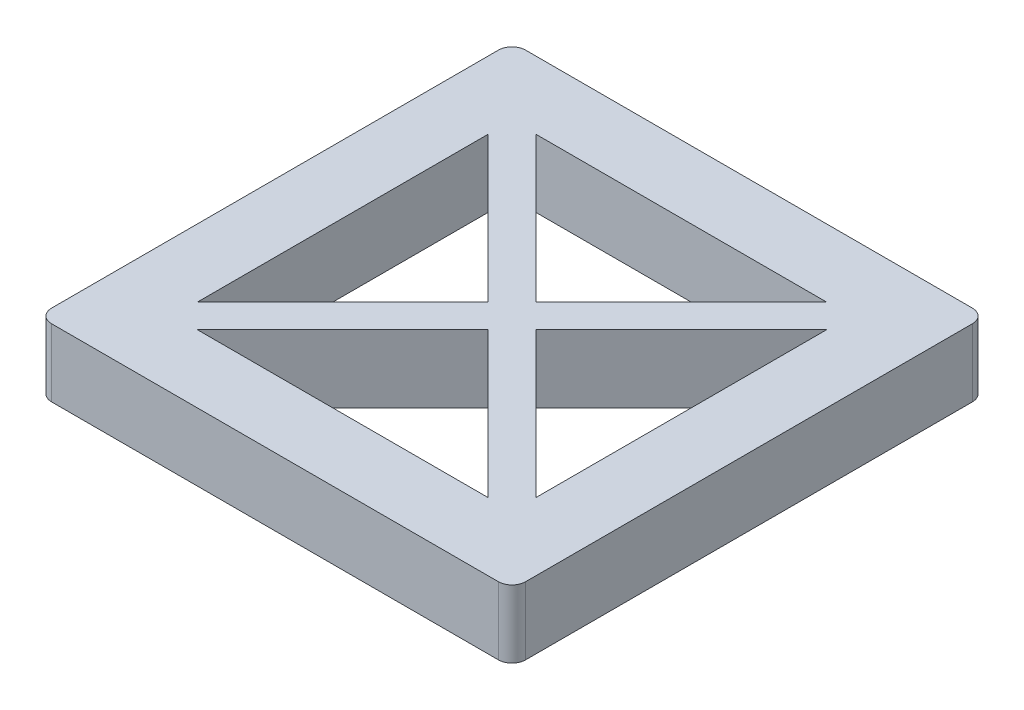
SolidWorks part; units mm, degrees
material "PVC 0.007 Plasticized"
ref_plane "Front Plane" through (0, 0, 0) normal (0, 0, 1) x (1, 0, 0)
ref_plane "Top Plane" through (0, 0, 0) normal (0, 1, 0) x (1, 0, 0)
ref_plane "Right Plane" through (0, 0, 0) normal (1, 0, 0) x (0, 0, -1)
sketch "Sketch1" plane through (0, 0, 0) normal (0, 1, 0) x (1, 0, 0)
  line L0 (6.35, 0) -> (6.35, -88.9) construction
  line L1 (0, 0) -> (88.9, 0)
  line L2 (0, 0) -> (0, -88.9)
  line L3 (0, -88.9) -> (88.9, -88.9)
  line L4 (88.9, 0) -> (88.9, -88.9)
  line L5 (12.7, -12.7) -> (76.2, -12.7)
  line L6 (12.7, -12.7) -> (12.7, -76.2)
  line L7 (12.7, -76.2) -> (76.2, -76.2)
  line L8 (76.2, -12.7) -> (76.2, -76.2)
  line L9 (82.55, 0) -> (82.55, -88.9) construction
  line L10 (0, -6.35) -> (88.9, -6.35) construction
  line L11 (0, -82.55) -> (88.9, -82.55) construction
  line L12 (12.7, -12.7) -> (76.2, -76.2)
  line L13 (12.7, -76.2) -> (76.2, -12.7)
  line L14 (14.9451, -78.4451) -> (78.4451, -14.9451)
  line L15 (10.4549, -14.9451) -> (73.9549, -78.4451)
  line L16 (10.4549, -73.9549) -> (73.9549, -10.4549)
  line L17 (14.9451, -10.4549) -> (78.4451, -73.9549)
  circle A0 centre (6.35, -6.35) radius 3.175
  circle A1 centre (6.35, -82.55) radius 3.175
  circle A2 centre (82.55, -82.55) radius 3.175
  circle A4 centre (82.55, -6.35) radius 3.175
  dimension "D9" = 6.35
  dimension "D10" = 6.35
  dimension "D11" = 6.35
  dimension "D12" = 3.175
  dimension "D13" = 6.35
  dimension "D1" = 12.7
  dimension "D2" = 12.7
  dimension "D3" = 12.7
  dimension "D4" = 12.7
  dimension "D5" = 6.35
  dimension "D6" = 6.35
  dimension "D7" = 6.35
  dimension "D8" = 6.35
  dimension "D14" = 76.2
  dimension "D15" = 76.2
  dimension "D16" = 3.175
extrude "Boss-Extrude1" add sketch "Sketch1" along normal blind 9.525
sketch "Sketch2" plane through (0, 9.525, 0) normal (0, 1, 0) x (1, 0, 0)
  line L4 (44.45, -48.9401) -> (71.7099, -76.2) construction
  line L5 (17.1901, -76.2) -> (44.45, -48.9401) construction
  line L6 (17.1901, -76.2) -> (71.7099, -76.2) construction
  line L7 (76.2, -17.1901) -> (76.2, -71.7099) construction
  line L20 (88.9, -88.9) -> (88.9, 0)
  line L21 (88.9, 0) -> (0, 0)
  line L22 (0, 0) -> (0, -88.9)
  line L23 (0, -88.9) -> (88.9, -88.9)
  line L24 (88.9, -88.9) -> (88.9, 0)
  line L25 (88.9, 0) -> (0, 0)
  line L26 (0, 0) -> (0, -88.9)
  line L27 (0, -88.9) -> (88.9, -88.9)
  line L28 (48.9401, -44.45) -> (76.2, -71.7099) construction
  line L29 (48.9401, -44.45) -> (76.2, -17.1901) construction
  line L30 (44.45, -39.9599) -> (71.7099, -12.7) construction
  line L31 (12.7, -71.7099) -> (39.9599, -44.45) construction
  line L32 (12.7, -17.1901) -> (12.7, -71.7099) construction
  line L33 (12.7, -17.1901) -> (39.9599, -44.45) construction
  line L34 (17.1901, -12.7) -> (71.7099, -12.7) construction
  line L35 (17.1901, -12.7) -> (44.45, -39.9599) construction
  line L36 (44.45, -48.9401) -> (71.7099, -76.2)
  line L37 (17.1901, -76.2) -> (44.45, -48.9401)
  line L38 (17.1901, -76.2) -> (71.7099, -76.2)
  line L39 (76.2, -17.1901) -> (76.2, -71.7099)
  line L40 (48.9401, -44.45) -> (76.2, -71.7099)
  line L41 (48.9401, -44.45) -> (76.2, -17.1901)
  line L42 (44.45, -39.9599) -> (71.7099, -12.7)
  line L43 (12.7, -71.7099) -> (39.9599, -44.45)
  line L44 (12.7, -17.1901) -> (12.7, -71.7099)
  line L45 (12.7, -17.1901) -> (39.9599, -44.45)
  line L46 (17.1901, -12.7) -> (71.7099, -12.7)
  line L47 (17.1901, -12.7) -> (44.45, -39.9599)
  dimension "D1" = 0
extrude "Boss-Extrude2" add sketch "Sketch2" along normal blind 3.175
fillet "Fillet1" radius 2.54 4 edges at (88.9, 6.35, 0) (0, 6.35, 0) (88.9, 6.35, 88.9) (0, 6.35, 88.9)
